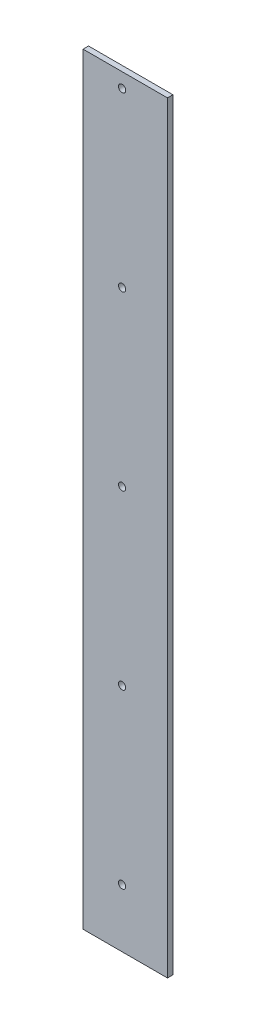
SolidWorks part; units mm, degrees
ref_plane "Front Plane" through (0, 0, 0) normal (0, 0, 1) x (1, 0, 0)
ref_plane "Top Plane" through (0, 0, 0) normal (0, 1, 0) x (1, 0, 0)
ref_plane "Right Plane" through (0, 0, 0) normal (1, 0, 0) x (0, 0, -1)
sketch "Sketch1" plane through (0, 0, 0) normal (0, 0, 1) x (1, 0, 0)
  line L0 (-22.6921, 203.279) -> (23.8079, 203.279)
  line L1 (-22.6921, 203.279) -> (-22.6921, -216.721)
  line L2 (-22.6921, -216.721) -> (23.8079, -216.721)
  line L3 (23.8079, 203.279) -> (23.8079, -216.721)
  line L4 (36.2236, -216.721) -> (-26.1921, -216.721) construction
  circle A0 centre (-1.1921, 195.279) radius 2 construction
  circle A1 centre (-1.1921, 195.279) radius 2
  circle A2 centre (-1.1921, 100.279) radius 2 construction
  circle A3 centre (-1.1921, 100.279) radius 2
  circle A4 centre (-1.1921, 5.279) radius 2 construction
  circle A5 centre (-1.1921, 5.279) radius 2
  circle A6 centre (-1.1921, -89.721) radius 2 construction
  circle A7 centre (-1.1921, -89.721) radius 2
  circle A8 centre (-1.1921, -184.721) radius 2 construction
  circle A9 centre (-1.1921, -184.721) radius 2
  dimension "D1" = 46.5
  dimension "D2" = 420
extrude "Boss-Extrude1" add sketch "Sketch1" along normal blind 3
